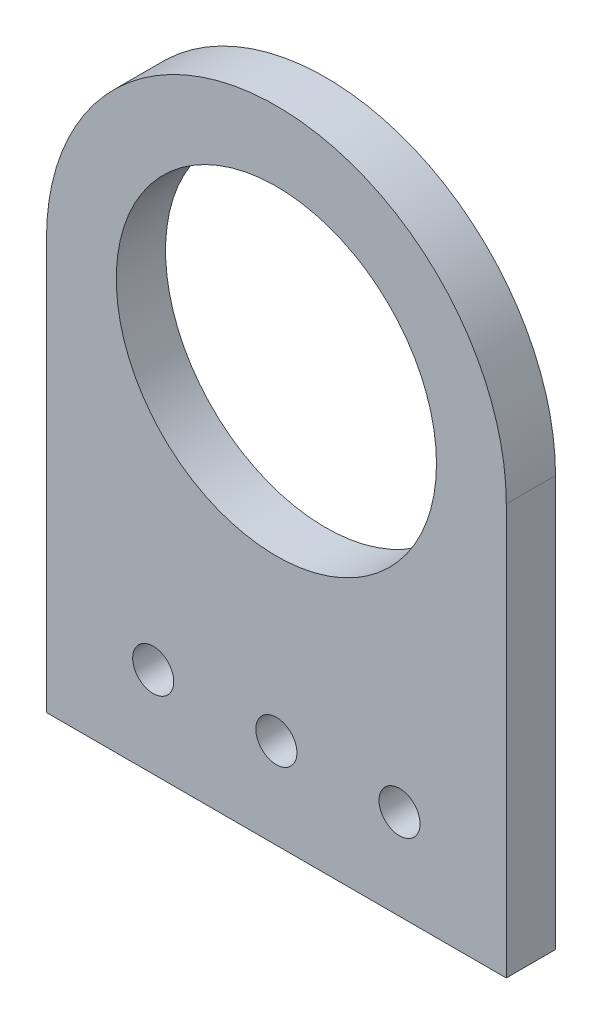
SolidWorks part; units mm, degrees
ref_plane "Alzado" through (0, 0, 0) normal (0, 0, 1) x (1, 0, 0)
ref_plane "Planta" through (0, 0, 0) normal (0, 1, 0) x (1, 0, 0)
ref_plane "Vista lateral" through (0, 0, 0) normal (1, 0, 0) x (0, 0, -1)
sketch "Croquis1" plane through (0, 0, 0) normal (0, 0, 1) x (1, 0, 0)
  line L0 (-14, 0) -> (14, 0) construction
  line L1 (0, 0) -> (0, -25) construction
  line L2 (-14, -25) -> (14, -25)
  line L3 (14, -25) -> (14, 0)
  line L4 (-14, -25) -> (-14, 0)
  circle A0 centre (0, 0) radius 9.75
  arc A1 (-14, 0) -> (14, 0) centre (0, 0) cw
  point P6 (0, 0)
  point P11 (0, -25)
extrude "Saliente-Extruir1" add sketch "Croquis1" along normal blind 3
sketch "Croquis2" plane through (0, 0, 3) normal (0, 0, 1) x (1, 0, 0)
  line L0 (0, -25) -> (0, -22) construction
  line L1 (-14, -25) -> (14, -25) construction
  line L2 (0, -22) -> (0, -19.5) construction
  circle A0 centre (0, -19.5) radius 1.25
  circle A1 centre (7.5, -19.5) radius 1.25
  circle A2 centre (-7.5, -19.5) radius 1.25
  dimension "D1" = 2
  dimension "D2" = 2
extrude "Cortar-Extruir1" cut sketch "Croquis2" against normal blind 3
